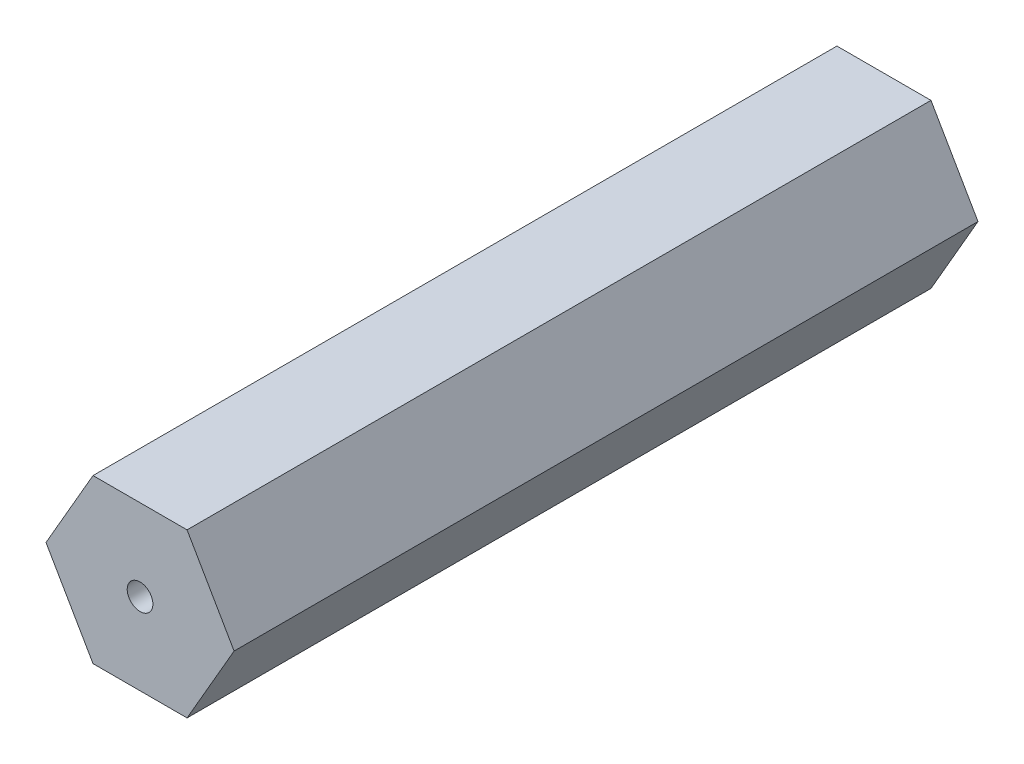
SolidWorks part; units mm, degrees
ref_plane "Front Plane" through (0, 0, 0) normal (0, 0, 1) x (1, 0, 0)
ref_plane "Top Plane" through (0, 0, 0) normal (0, 1, 0) x (1, 0, 0)
ref_plane "Right Plane" through (0, 0, 0) normal (1, 0, 0) x (0, 0, -1)
sketch "Sketch1" plane through (0, 0, 0) normal (0, 0, 1) x (1, 0, 0)
  line L1 (7.3323, 0) -> (3.6662, 6.35)
  line L2 (3.6662, 6.35) -> (-3.6662, 6.35)
  line L3 (-3.6662, 6.35) -> (-7.3323, 0)
  line L4 (-7.3323, 0) -> (-3.6662, -6.35)
  line L5 (-3.6662, -6.35) -> (3.6662, -6.35)
  line L6 (3.6662, -6.35) -> (7.3323, 0)
  circle A0 centre (0, 0) radius 6.35 construction
  dimension "D1" = 12.7
extrude "Boss-Extrude1" add sketch "Sketch1" along normal blind 58
sketch "Sketch2" plane through (0, 0, 58) normal (0, 0, 1) x (1, 0, 0)
  circle A0 centre (0, 0) radius 1
  dimension "D1" = 2
extrude "Cut-Extrude1" cut sketch "Sketch2" against normal through all
